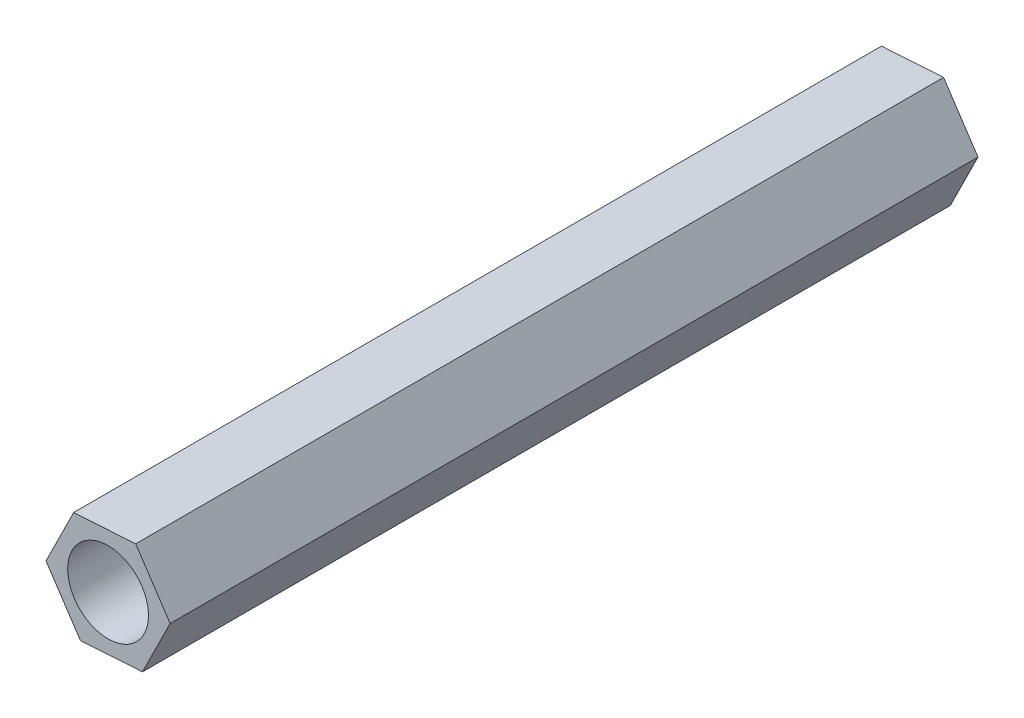
SolidWorks part; units mm, degrees
ref_plane "前视基准面" through (0, 0, 0) normal (0, 0, 1) x (1, 0, 0)
ref_plane "上视基准面" through (0, 0, 0) normal (0, 1, 0) x (1, 0, 0)
ref_plane "右视基准面" through (0, 0, 0) normal (1, 0, 0) x (0, 0, -1)
sketch "草图1" plane through (0, 0, 0) normal (0, 0, 1) x (1, 0, 0)
  line L1 (1.0263, 2.0688) -> (-1.2785, 1.9232)
  line L2 (-1.2785, 1.9232) -> (-2.3048, -0.1456)
  line L3 (-2.3048, -0.1456) -> (-1.0263, -2.0688)
  line L4 (-1.0263, -2.0688) -> (1.2785, -1.9232)
  line L5 (1.2785, -1.9232) -> (2.3048, 0.1456)
  line L6 (2.3048, 0.1456) -> (1.0263, 2.0688)
  circle A0 centre (0, 0) radius 2 construction
  dimension "D1" = 4
extrude "凸台-拉伸1" add sketch "草图1" along normal blind 30
sketch "草图2" plane through (0, 0, 0) normal (0, 0, -1) x (-1, 0, 0)
  circle A0 centre (0, 0) radius 1.5
  dimension "D1" = 3
extrude "切除-拉伸1" cut sketch "草图2" against normal through all
